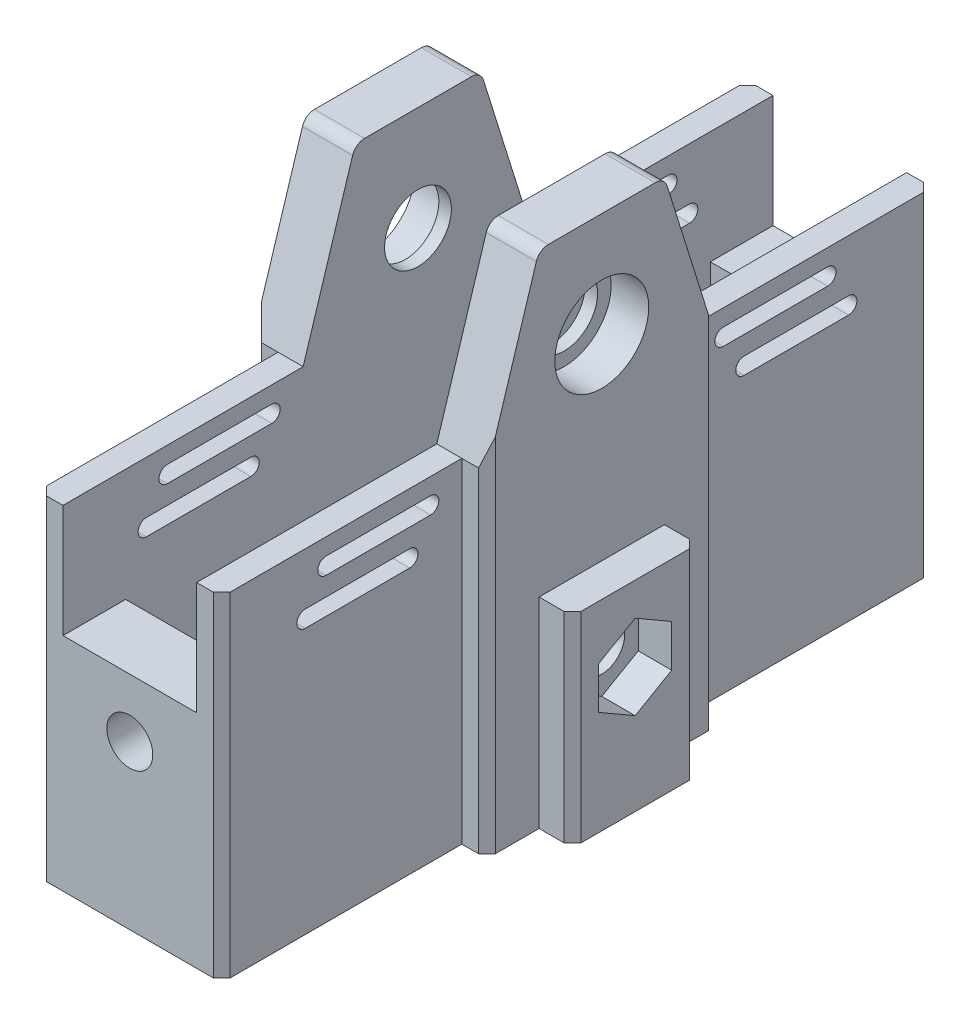
SolidWorks part; units mm, degrees
ref_plane "Front Plane" through (0, 0, 0) normal (0, 0, 1) x (1, 0, 0)
ref_plane "Top Plane" through (0, 0, 0) normal (0, 1, 0) x (1, 0, 0)
ref_plane "Right Plane" through (0, 0, 0) normal (1, 0, 0) x (0, 0, -1)
sketch "Sketch1" plane through (0, 0, 0) normal (1, 0, 0) x (0, 0, -1)
  line L5 (0, 0) -> (0, 80)
  line L9 (112.5, 80) -> (170, 80)
  line L10 (170, 80) -> (170, 0)
  line L11 (170, 0) -> (0, 0)
  line L12 (0, 80) -> (57.5, 80)
  line L13 (57.5, 80) -> (70, 120)
  line L14 (70, 120) -> (100, 120)
  line L15 (100, 120) -> (112.5, 80)
  point P4 (85, 0)
  point P13 (85, 120)
  dimension "D1" = 80
  dimension "D2" = 170
  dimension "D3" = 55
  dimension "D4" = 30
  dimension "D5" = 80
  dimension "D6" = 120
extrude "Boss-Extrude1" add sketch "Sketch1" along normal blind 56
sketch "Sketch5" plane through (0, 0, -170) normal (0, 0, -1) x (-1, 0, 0)
  line L0 (-56, 120) -> (0, 120) construction
  line L1 (-44, 120) -> (-12, 120)
  line L2 (-44, 120) -> (-44, 13)
  line L3 (-44, 13) -> (-12, 13)
  line L4 (-12, 120) -> (-12, 13)
  line L6 (0, 0) -> (0, 80) construction
  line L7 (-56, 0) -> (-56, 80) construction
  line L8 (-56, 0) -> (0, 0) construction
  dimension "D1" = 12
  dimension "D2" = 12
  dimension "D3" = 13
extrude "Cut-Extrude2" cut sketch "Sketch5" against normal through all
sketch "Sketch6" plane through (56, 0, 0) normal (1, 0, 0) x (0, 0, -1)
  line L8 (0, 0) -> (170, 0)
  line L9 (170, 0) -> (170, 80)
  line L10 (170, 80) -> (112.5, 80)
  line L11 (112.5, 80) -> (100, 120)
  line L12 (100, 120) -> (70, 120)
  line L13 (70, 120) -> (57.5, 80)
  line L14 (57.5, 80) -> (0, 80)
  line L15 (0, 80) -> (0, 0)
  line L16 (0, 0) -> (170, 0)
  line L17 (170, 0) -> (170, 80)
  line L18 (170, 80) -> (112.5, 80)
  line L19 (112.5, 80) -> (100, 120)
  line L20 (100, 120) -> (70, 120)
  line L21 (70, 120) -> (57.5, 80)
  line L22 (57.5, 80) -> (0, 80)
  line L23 (0, 80) -> (0, 0)
  circle A0 centre (85, 95) radius 11.25
  point P6 (85, 120)
  dimension "D2" = 22.5
  dimension "D3" = 25
  dimension "D1" = 0
extrude "Cut-Extrude3" cut sketch "Sketch6" against normal through all contours A0
sketch "Sketch7" plane through (0, 13, 0) normal (0, 1, 0) x (1, 0, 0)
  line L0 (0, 85) -> (56, 85) construction
  line L1 (12, 170) -> (44, 170)
  line L2 (12, 170) -> (12, 155)
  line L3 (12, 155) -> (44, 155)
  line L4 (44, 170) -> (12, 170)
  line L5 (12, 170) -> (12, 0)
  line L6 (12, 0) -> (44, 0)
  line L7 (44, 0) -> (44, 170)
  line L8 (44, 170) -> (12, 170)
  line L9 (12, 170) -> (12, 0)
  line L10 (12, 0) -> (44, 0)
  line L11 (44, 0) -> (44, 170)
  line L12 (44, 170) -> (44, 155)
  line L13 (0, 100) -> (0, 70) construction
  line L14 (56, 100) -> (56, 70) construction
  line L15 (12, 15) -> (44, 15)
  line L16 (44, 0) -> (44, 15)
  line L17 (12, 0) -> (44, 0)
  line L18 (12, 0) -> (12, 15)
  line M10 (44, 170) -> (12, 170)
  line M11 (12, 170) -> (12, 0)
  line M12 (12, 0) -> (44, 0)
  line M13 (44, 0) -> (44, 170)
  dimension "D2" = 15
  dimension "D1" = 0
extrude "Boss-Extrude2" add sketch "Sketch7" along normal blind 40 contours L3 M11 M13 M10 | L15 L9 M12 M13
sketch "Sketch9" plane through (0, 0, -170) normal (0, 0, -1) x (-1, 0, 0)
  line L0 (-56, 0) -> (0, 0) construction
  line L1 (-44, 53) -> (-12, 53) construction
  circle A0 centre (-28, 39) radius 5.5
  point P2 (-28, 0)
  dimension "D1" = 11
  dimension "D2" = 14
extrude "Cut-Extrude5" cut sketch "Sketch9" against normal through all
sketch "Sketch10" plane through (0, 0, 0) normal (-1, 0, 0) x (0, 0, 1)
  line L0 (0, 0) -> (-170, 0) construction
  line L1 (-170, 0) -> (-170, 80) construction
  line L2 (-85, 120) -> (-85, 0) construction
  line L3 (-100, 120) -> (-70, 120) construction
  line L4 (-120, 74) -> (-145, 74) construction
  line L5 (-120, 72) -> (-145, 72)
  line L6 (-120, 76) -> (-145, 76)
  line L7 (-125, 65.5029) -> (-150, 65.5029) construction
  line L8 (-125, 63.5029) -> (-150, 63.5029)
  line L9 (-125, 67.5029) -> (-150, 67.5029)
  line L10 (-45, 65.5029) -> (-20, 65.5029) construction
  line L11 (-45, 63.5029) -> (-20, 63.5029)
  line L12 (-45, 67.5029) -> (-20, 67.5029)
  line L13 (-50, 74) -> (-25, 74) construction
  line L14 (-50, 72) -> (-25, 72)
  line L15 (-50, 76) -> (-25, 76)
  circle A0 centre (-108.7515, 74) radius 1.5
  circle A1 centre (-113, 65.5029) radius 1.5
  circle A2 centre (-57, 65.5029) radius 1.5
  circle A3 centre (-61.2485, 74) radius 1.5
  arc A4 (-120, 72) -> (-120, 76) centre (-120, 74) ccw
  arc A5 (-145, 76) -> (-145, 72) centre (-145, 74) ccw
  arc A6 (-125, 63.5029) -> (-125, 67.5029) centre (-125, 65.5029) ccw
  arc A7 (-150, 67.5029) -> (-150, 63.5029) centre (-150, 65.5029) ccw
  circle A8 centre (-57, 65.5029) radius 1.5
  circle A9 centre (-61.2485, 74) radius 1.5
  arc A10 (-45, 63.5029) -> (-45, 67.5029) centre (-45, 65.5029) cw
  arc A11 (-20, 67.5029) -> (-20, 63.5029) centre (-20, 65.5029) cw
  arc A12 (-50, 72) -> (-50, 76) centre (-50, 74) cw
  arc A13 (-25, 76) -> (-25, 72) centre (-25, 74) cw
  point P19 (-132.5, 74)
  point P26 (-137.5, 65.5029)
  point P35 (-32.5, 65.5029)
  point P42 (-37.5, 74)
  dimension "D3" = 3
  dimension "D6" = 3
  dimension "D1" = 57
  dimension "D2" = 74
  dimension "D4" = 9.5
  dimension "D5" = 8.4971
  dimension "D7" = 4
  dimension "D8" = 4
  dimension "D9" = 25
  dimension "D10" = 25
  dimension "D11" = 25
  dimension "D12" = 20
extrude "Cut-Extrude6" cut sketch "Sketch10" against normal through all contours L6 A5 L5 A4 | L9 A7 L8 A6 | A13 L15 A12 L14 | A11 L12 A10 L11
sketch "Sketch21" plane through (0, 80, 0) normal (0, 1, 0) x (1, 0, 0)
  line L0 (28, 170) -> (28, 0) construction
  line L1 (0, 170) -> (5.9113, 170)
  line L2 (0, 170) -> (0, 112.5)
  line L3 (0, 112.5) -> (5.9113, 112.5)
  line L4 (5.9113, 170) -> (5.9113, 112.5)
  line L5 (44, 170) -> (12, 170) construction
  line L6 (12, 0) -> (44, 0) construction
  line L7 (12, 57.5) -> (0, 57.5) construction
  line L8 (0, 0) -> (6, 0)
  line L9 (0, 0) -> (0, 57.5)
  line L10 (0, 57.5) -> (6, 57.5)
  line L11 (6, 0) -> (6, 57.5)
  line L12 (12, 112.5) -> (0, 112.5) construction
  line L13 (56, 0) -> (44, 0) construction
  line L14 (56, 112.5) -> (50.0887, 112.5)
  line L15 (50.0887, 170) -> (50.0887, 112.5)
  line L16 (56, 170) -> (50.0887, 170)
  line L17 (56, 170) -> (56, 112.5)
  line L22 (56, 57.5) -> (50, 57.5)
  line L23 (56, 57.5) -> (56, 0)
  line L24 (56, 0) -> (50, 0)
  line L25 (50, 57.5) -> (50, 0)
  point P20 (2.9557, 112.5)
extrude "Cut-Extrude13" cut sketch "Sketch21" against normal up to next
sketch "Sketch23" plane through (12, 0, 0) normal (1, 0, 0) x (0, 0, -1)
  circle A0 centre (85, 95) radius 11.25
extrude "Boss-Extrude3" add sketch "Sketch23" against normal blind 3
sketch "Sketch26" plane through (44, 0, 0) normal (-1, 0, 0) x (0, 0, 1)
  circle A0 centre (-85, 95) radius 11.25
extrude "Boss-Extrude5" add sketch "Sketch26" against normal blind 3 separate body
sketch "Sketch28" plane through (9, 0, 0) normal (-1, 0, 0) x (0, 0, 1)
  circle A0 centre (-85, 95) radius 8
  dimension "D1" = 16
extrude "Cut-Extrude16" cut sketch "Sketch28" along direction (-1, 0, 0) on the side against the normal up to surface (47 mm away) contours A0
ref_plane "Plane1" through (28, 0, 0) normal (-1, 0, 0) x (0, 0, 1)
sketch "Sketch29" plane through (56, 0, 0) normal (1, 0, 0) x (0, 0, -1)
  line L0 (70, 0) -> (70, 48)
  line L1 (57.5, 0) -> (112.5, 0) construction
  line L2 (70, 48) -> (100, 48)
  line L3 (100, 48) -> (100, 0)
  line L4 (70, 0) -> (100, 0)
  point P4 (85, 48)
  point P10 (85, 0)
  dimension "D1" = 30
  dimension "D2" = 48
extrude "Boss-Extrude6" add sketch "Sketch29" along normal blind 8
sketch "Sketch31" plane through (64, 0, 0) normal (1, 0, 0) x (0, 0, -1)
  line L0 (70, 0) -> (100, 0) construction
  line L1 (76.25, 24.9482) -> (85, 19.8964)
  line L2 (85, 19.8964) -> (93.75, 24.9482)
  line L3 (93.75, 24.9482) -> (93.75, 35.0518)
  line L4 (93.75, 35.0518) -> (85, 40.1036)
  line L5 (85, 40.1036) -> (76.25, 35.0518)
  line L6 (76.25, 35.0518) -> (76.25, 24.9482)
  line L16 (70, 0) -> (70, 48)
  line L17 (70, 0) -> (70, 48)
  line L18 (70, 48) -> (100, 48)
  line L19 (70, 48) -> (100, 48)
  line L20 (100, 48) -> (100, 0)
  line L21 (100, 48) -> (100, 0)
  line L22 (100, 0) -> (112.5, 0)
  line L23 (100, 0) -> (112.5, 0)
  line L24 (112.5, 0) -> (112.5, 80)
  line L25 (112.5, 0) -> (112.5, 80)
  line L26 (112.5, 80) -> (100, 120)
  line L27 (112.5, 80) -> (100, 120)
  line L28 (100, 120) -> (70, 120)
  line L29 (100, 120) -> (70, 120)
  line L30 (70, 120) -> (57.5, 80)
  line L31 (70, 120) -> (57.5, 80)
  line L32 (57.5, 80) -> (57.5, 0)
  line L33 (57.5, 80) -> (57.5, 0)
  line L34 (57.5, 0) -> (70, 0)
  line L35 (57.5, 0) -> (70, 0)
  circle A0 centre (85, 30) radius 8.75 construction
  dimension "D2" = 17.5
  dimension "D3" = 30
  dimension "D1" = 0
extrude "Cut-Extrude18" cut sketch "Sketch31" against normal blind 8
sketch "Sketch32" plane through (56, 0, 0) normal (1, 0, 0) x (0, 0, -1)
  line L0 (93.75, 24.9482) -> (93.75, 35.0518) construction
  circle A0 centre (85, 30) radius 5.5
  point P6 (93.75, 30)
  dimension "D2" = 11
extrude "Cut-Extrude19" cut sketch "Sketch32" against normal up to next (12 mm away)
mirror "Mirror3" about plane through (28, 0, 0) normal (-1, 0, 0) of "Boss-Extrude6"
mirror "Mirror4" about plane through (28, 0, 0) normal (-1, 0, 0) of "Cut-Extrude19", "Cut-Extrude18"
chamfer "Chamfer1" distance 2 angle 45 12 edges at (6, 40, 0) (0, 40, -57.5) (-8, 24, -70) (-8, 24, -100) (0, 40, -112.5) (5.9113, 40, -170) (50.0887, 40, -170) (50, 40, 0) (64, 24, -70) (56, 40, -57.5) (56, 40, -112.5) (64, 24, -100)
sketch "Sketch34" plane through (0, 13, 0) normal (0, 1, 0) x (1, 0, 0)
  line L0 (-8, 85) -> (56, 85) construction
  line L1 (38.592, 122.5) -> (18.592, 122.5)
  line L2 (38.592, 122.5) -> (38.592, 137.5)
  line L3 (38.592, 137.5) -> (18.592, 137.5)
  line L4 (18.592, 122.5) -> (18.592, 137.5)
  line L5 (38.592, 122.5) -> (18.592, 137.5) construction
  line L6 (38.592, 137.5) -> (18.592, 122.5) construction
  line L7 (-8, 98) -> (-8, 72) construction
  line L8 (56, 100) -> (56, 70) construction
  line L9 (38.592, 32.5) -> (18.592, 32.5)
  line L10 (18.592, 47.5) -> (18.592, 32.5)
  line L11 (38.592, 47.5) -> (18.592, 47.5)
  line L12 (38.592, 47.5) -> (38.592, 32.5)
  point P0 (28.592, 130)
  dimension "D1" = 15
  dimension "D2" = 20
  dimension "D3" = 130
extrude "Cut-Extrude20" cut sketch "Sketch34" against normal up to next (13 mm away)
fillet "Fillet1" radius 3 8 edges at (18.592, 6.5, -32.5) (38.592, 6.5, -32.5) (18.592, 6.5, -47.5) (38.592, 6.5, -47.5) (18.592, 6.5, -122.5) (38.592, 6.5, -122.5) (18.592, 6.5, -137.5) (38.592, 6.5, -137.5)
fillet "Fillet2" radius 3 4 edges at (50, 120, -70) (50, 120, -100) (6, 120, -100) (6, 120, -70)
